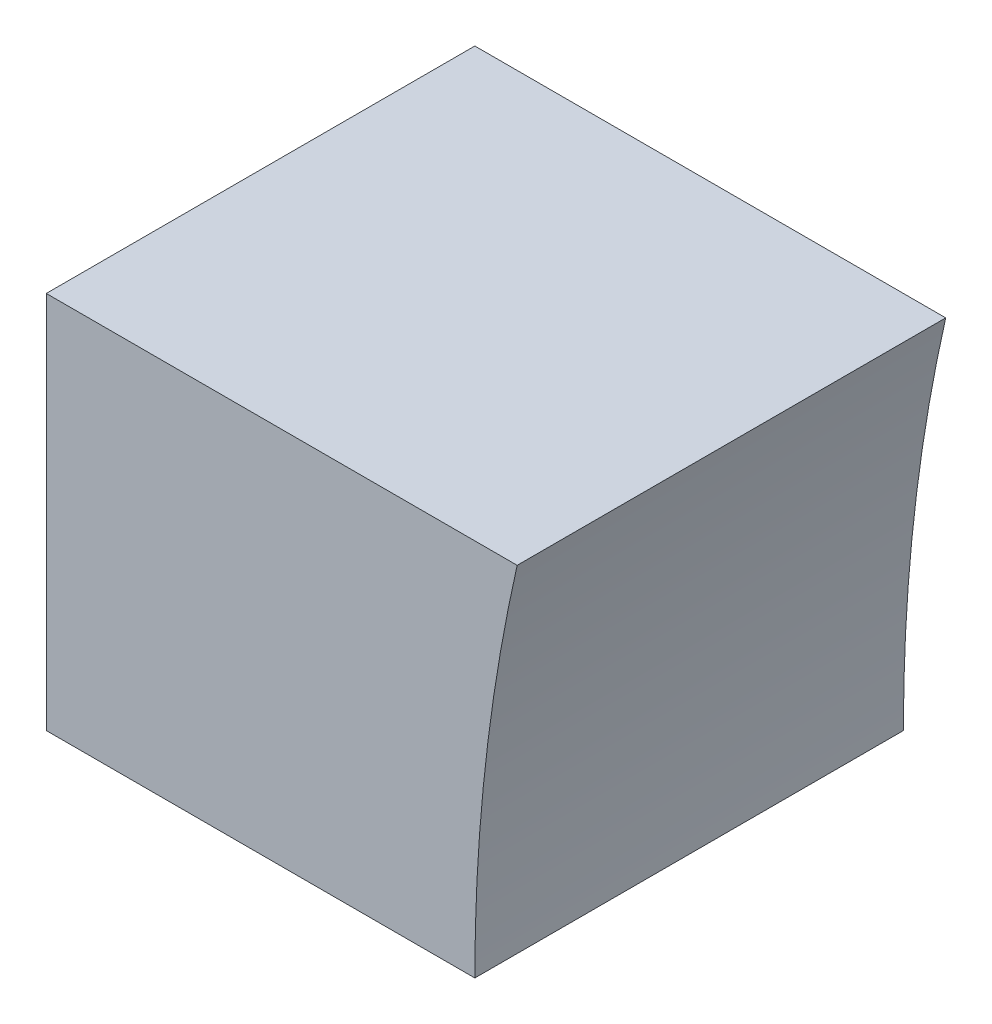
SolidWorks part; units mm, degrees
material "砖"
ref_plane "前视基准面" through (0, 0, 0) normal (0, 0, 1) x (1, 0, 0)
ref_plane "上视基准面" through (0, 0, 0) normal (0, 1, 0) x (1, 0, 0)
ref_plane "右视基准面" through (0, 0, 0) normal (1, 0, 0) x (0, 0, -1)
sketch "草图1" plane through (0, 0, 0) normal (0, 0, 1) x (1, 0, 0)
  line L0 (-4560, 0) -> (-7920, 0)
  line L1 (-12480, 7680) -> (0, 7680)
  line L2 (-12480, 7680) -> (-12480, 0)
  line L3 (-12480, 0) -> (0, 0)
  line L4 (0, 7680) -> (0, 0)
  line L5 (-7920, 0) -> (-7920, 3840)
  line L6 (-7920, 3840) -> (-4560, 3840)
  line L7 (-4560, 3840) -> (-4560, 0)
  line L8 (-7920, 3840) -> (-8160, 3840)
  line L9 (-4560, 3840) -> (-4320, 3840)
  line L10 (-7837.7749, 4359.1486) -> (-8066.0285, 4433.3126)
  line L11 (-7599.1486, 4827.4792) -> (-7793.3126, 4968.5477)
  line L12 (-7227.4792, 5199.1486) -> (-7368.5477, 5393.3126)
  line L13 (-6759.1486, 5437.7749) -> (-6833.3126, 5666.0285)
  line L14 (-6240, 5520) -> (-6240, 5760)
  line L15 (-5720.8514, 5437.7749) -> (-5646.6874, 5666.0285)
  line L16 (-5252.5208, 5199.1486) -> (-5111.4523, 5393.3126)
  line L17 (-4880.8514, 4827.4792) -> (-4686.6874, 4968.5477)
  line L18 (-4642.2251, 4359.1486) -> (-4413.9715, 4433.3126)
  line L19 (-4560, 3840) -> (-4320, 3840)
  line L20 (-4573.7633, 3298.6069) -> (-4560, 3294.1349)
  line L21 (-6833.3126, 5666.0285) -> (-6928.8298, 5960)
  line L22 (-5683.7694, 5551.9017) -> (-5551.1702, 5960)
  line L23 (-5551.1702, 5960) -> (-6928.8298, 5960)
  line L24 (-7920, 0) -> (-9123.3069, 0)
  line L25 (-8160, 0) -> (-8640, 0)
  line L26 (-8160, 0) -> (-8640, 0)
  line L27 (-8640, 3840) -> (-8160, 3840)
  line L28 (-8640, 3840) -> (-8640, 4264)
  line L29 (-7837.7749, 3320.8514) -> (-7920, 3294.1349) [skipped]
  line L30 (-7599.1486, 2852.5208) -> (-7793.3126, 2711.4523) [skipped]
  line L31 (-7227.4792, 2480.8514) -> (-7368.5477, 2286.6874) [skipped]
  line L32 (-6759.1486, 2242.2251) -> (-6833.3126, 2013.9715) [skipped]
  line L33 (-6240, 2160) -> (-6240, 1920) [skipped]
  line L34 (-5720.8514, 2242.2251) -> (-5646.6874, 2013.9715) [skipped]
  line L35 (-5252.5208, 2480.8514) -> (-5111.4523, 2286.6874) [skipped]
  line L36 (-4880.8514, 2852.5208) -> (-4686.6874, 2711.4523) [skipped]
  line L37 (-8640, 4264) -> (-8112.5982, 4264)
  line L38 (-8112.5982, 4264) -> (-8592.5982, 4264)
  line L39 (-8592.5982, 4264) -> (-8592.5982, 4688)
  line L40 (-8592.5982, 4688) -> (-7962.5841, 4688)
  line L41 (-7962.5841, 4688) -> (-8442.5841, 4688)
  line L42 (-8442.5841, 4688) -> (-8442.5841, 5112)
  line L43 (-8442.5841, 5112) -> (-7678.1989, 5112)
  line L44 (-7678.1989, 5112) -> (-8158.1989, 5112)
  line L45 (-8158.1989, 5112) -> (-8158.1989, 5536)
  line L46 (-8158.1989, 5536) -> (-7139.9911, 5536)
  line L47 (-7139.9911, 5536) -> (-7619.9911, 5536)
  line L48 (-7619.9911, 5536) -> (-7619.9911, 5960)
  line L49 (-7619.9911, 5960) -> (-6928.8298, 5960)
  arc A0 (-4560, 3840) -> (-7920, 3840) centre (-6240, 3840) ccw
  arc A1 (-4320, 3840) -> (-8160, 3840) centre (-6240, 3840) ccw
  point P7 (-6240, 0)
  point P56 (-6240, 3840)
  dimension "D5" = 3840
  dimension "D1" = 12480
  dimension "D2" = 7680
  dimension "D3" = 3360
  dimension "D4" = 3840
  dimension "D7" = 240
  dimension "D8" = 480
  dimension "D9" = 424
  dimension "D10" = 720
  dimension "D11" = 480
  dimension "D12" = 480
  dimension "D13" = 480
  dimension "D14" = 480
  dimension "D6" = 20
extrude "凸台-拉伸1" add sketch "草图1" along normal blind 480 contours A1 L37 L28 L27
scale "缩放比例1" scale about origin uniform scaling yes scale factor 1.3
